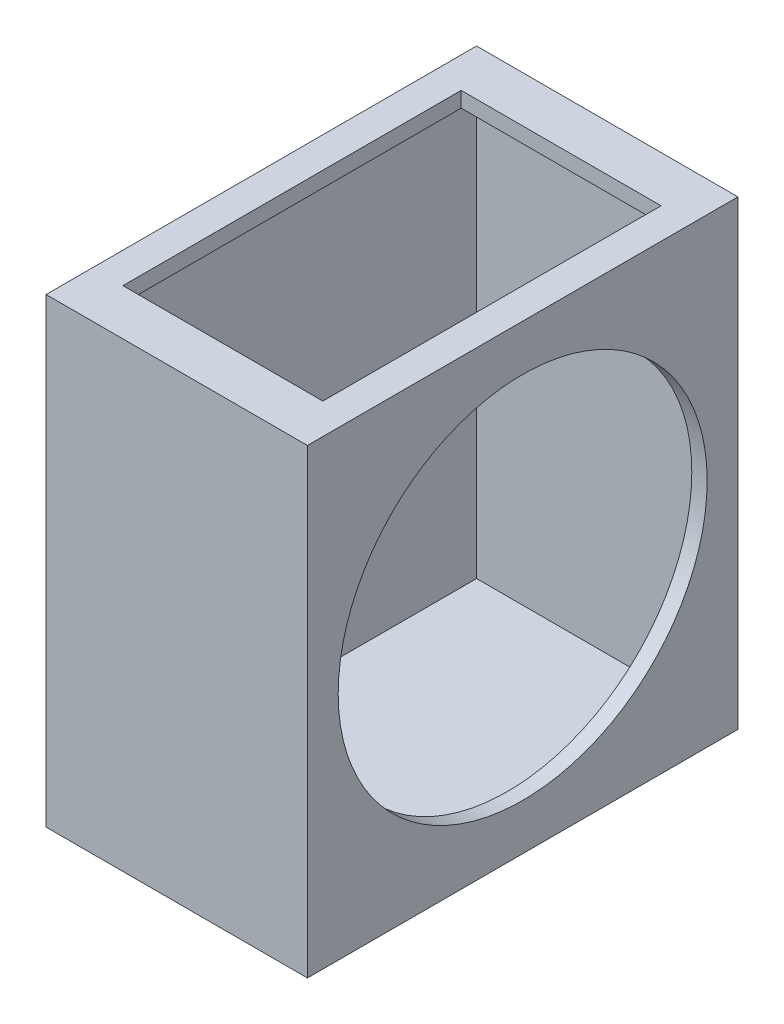
SolidWorks part; units mm, degrees
ref_plane "Front Plane" through (0, 0, 0) normal (0, 0, 1) x (1, 0, 0)
ref_plane "Top Plane" through (0, 0, 0) normal (0, 1, 0) x (1, 0, 0)
ref_plane "Right Plane" through (0, 0, 0) normal (1, 0, 0) x (0, 0, -1)
sketch "Sketch1" plane through (0, 0, 0) normal (0, 0, 1) x (1, 0, 0)
  line L1 (-4.25, -7.5) -> (4.25, -7.5)
  line L2 (-4.25, -7.5) -> (-4.25, 7.5)
  line L3 (-4.25, 7.5) -> (4.25, 7.5)
  line L4 (4.25, -7.5) -> (4.25, 7.5)
  line L5 (-4.25, -7.5) -> (4.25, 7.5) construction
  line L6 (-4.25, 7.5) -> (4.25, -7.5) construction
  point P0 (0, 0)
  dimension "D1" = 8.5
  dimension "D2" = 15
extrude "Boss-Extrude1" add sketch "Sketch1" along normal blind 14
shell "Shell3" thickness 0.5
sketch "Sketch2" plane through (4.25, 0, 0) normal (1, 0, 0) x (0, 0, -1)
  line L1 (-14, -7.5) -> (0, -7.5)
  line L2 (-14, -7.5) -> (-14, 7.5)
  line L3 (-14, 7.5) -> (0, 7.5)
  line L4 (0, -7.5) -> (0, 7.5)
  line L5 (-14, -7.5) -> (0, 7.5) construction
  line L6 (-14, 7.5) -> (0, -7.5) construction
  circle A0 centre (-7, 0) radius 6
  point P0 (-7, 0)
  dimension "D2" = 12
  dimension "D1" = 14
extrude "Boss-Extrude2" add sketch "Sketch2" against normal blind 0.5
sketch "Sketch3" plane through (0, 7.5, 0) normal (0, 1, 0) x (1, 0, 0)
  line L0 (-4.25, -14) -> (-4.25, 0) construction
  line L1 (-3.25, -12.5) -> (3.25, -12.5)
  line L2 (-3.25, -12.5) -> (-3.25, -1.5)
  line L3 (-3.25, -1.5) -> (3.25, -1.5)
  line L4 (3.25, -12.5) -> (3.25, -1.5)
  line L5 (-3.25, -12.5) -> (3.25, -1.5) construction
  line L6 (-3.25, -1.5) -> (3.25, -12.5) construction
  line L7 (4.25, -14) -> (4.25, 0) construction
  line L8 (4.25, 0) -> (-4.25, 0) construction
  point P0 (0, -7)
  point P7 (-4.25, -7)
  dimension "D1" = 1
  dimension "D2" = 1.5
extrude "Cut-Extrude1" cut sketch "Sketch3" against normal up to surface (0.5 mm away) up to face at (0, 7, 7)
scale "Scale1" scale about centroid uniform scaling yes scale factor 10
